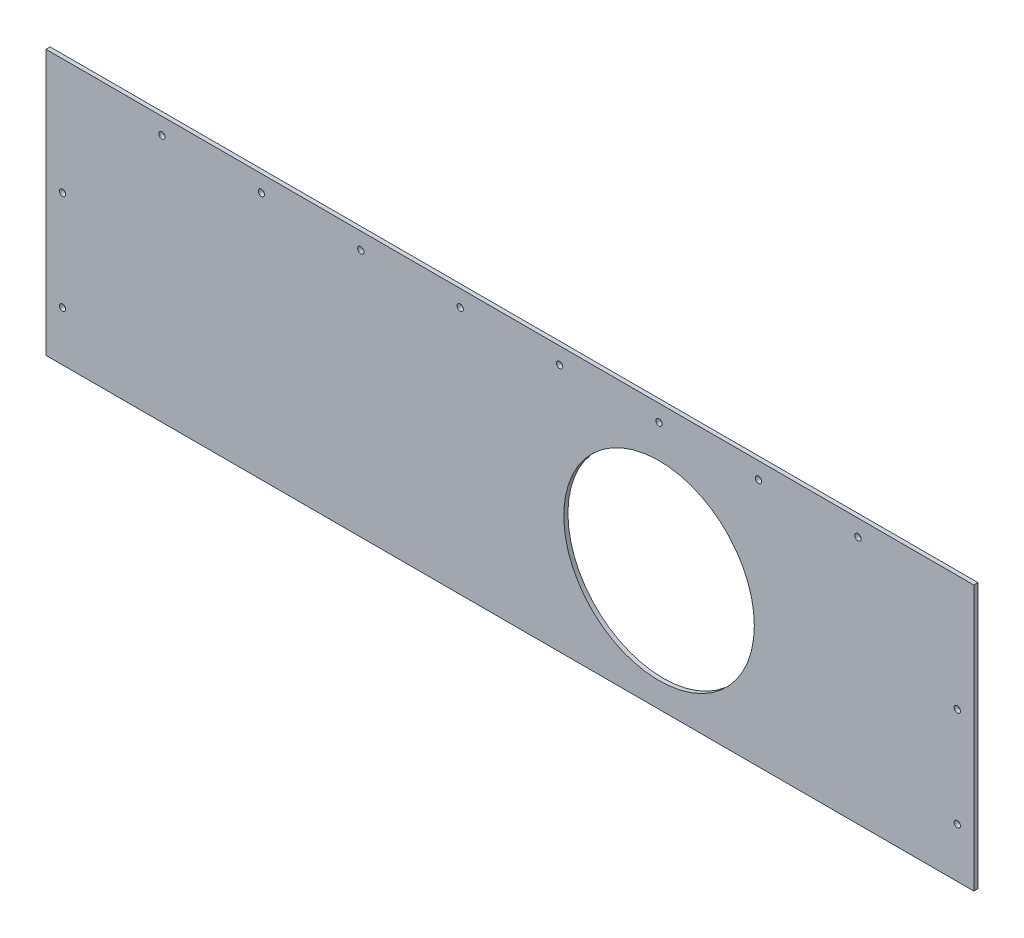
SolidWorks part; units mm, degrees
ref_plane "Front Plane" through (0, 0, 0) normal (0, 0, 1) x (1, 0, 0)
ref_plane "Top Plane" through (0, 0, 0) normal (0, 1, 0) x (1, 0, 0)
ref_plane "Right Plane" through (0, 0, 0) normal (1, 0, 0) x (0, 0, -1)
sketch "Sketch1" plane through (0, 0, 0) normal (0, 0, 1) x (1, 0, 0)
  line L1 (0, 0) -> (711.2, 0)
  line L2 (0, 0) -> (0, 203.2)
  line L3 (0, 203.2) -> (711.2, 203.2)
  line L4 (711.2, 0) -> (711.2, 203.2)
  dimension "D1" = 203.2
  dimension "D2" = 711.2
extrude "Boss-Extrude1" add sketch "Sketch1" along normal blind 3.175
sketch "Sketch2" plane through (0, 0, 3.175) normal (0, 0, 1) x (1, 0, 0)
  line L0 (0, 190.5) -> (711.2, 190.5) construction
  line L1 (0, 203.2) -> (0, 0) construction
  line L2 (711.2, 0) -> (711.2, 203.2) construction
  line L4 (711.2, 203.2) -> (0, 203.2) construction
  line L5 (698.5, 203.2) -> (698.5, 0) construction
  line L7 (12.7, 203.2) -> (12.7, 0) construction
  line L8 (0, 0) -> (711.2, 0) construction
  circle A0 centre (698.5, 190.5) radius 2.413 construction
  circle A1 centre (12.7, 190.5) radius 2.413 construction
  circle A2 centre (12.7, 114.3) radius 2.413
  circle A3 centre (698.5, 114.3) radius 2.413
  circle A4 centre (12.7, 38.1) radius 2.413
  circle A5 centre (698.5, 38.1) radius 2.413
  circle A6 centre (88.9, 190.5) radius 2.413
  circle A7 centre (165.1, 190.5) radius 2.413
  circle A8 centre (241.3, 190.5) radius 2.413
  circle A9 centre (622.3, 190.5) radius 2.413
  circle A10 centre (546.1, 190.5) radius 2.413
  circle A11 centre (469.9, 190.5) radius 2.413
  circle A12 centre (393.7, 190.5) radius 2.413
  circle A13 centre (317.5, 190.5) radius 2.413
  point P14 (12.7, 190.5)
  point P15 (698.5, 190.5)
  dimension "D4" = 4.826
  dimension "D5" = 4.826
  dimension "D1" = 12.7
  dimension "D2" = 12.7
  dimension "D3" = 12.7
  dimension "D6" = 3
  dimension "D7" = 5
  dimension "D8" = 5
extrude "Cut-Extrude1" cut sketch "Sketch2" against normal up to next
sketch "Sketch3" plane through (0, 0, 3.175) normal (0, 0, 1) x (1, 0, 0)
  line L0 (711.2, 0) -> (711.2, 203.2) construction
  line L5 (0, 0) -> (711.2, 0) construction
  circle A1 centre (469.9, 92.075) radius 73.025
  dimension "D1" = 146.05
  dimension "D3" = 92.075
  dimension "D2" = 241.3
extrude "Cut-Extrude2" cut sketch "Sketch3" against normal up to next
